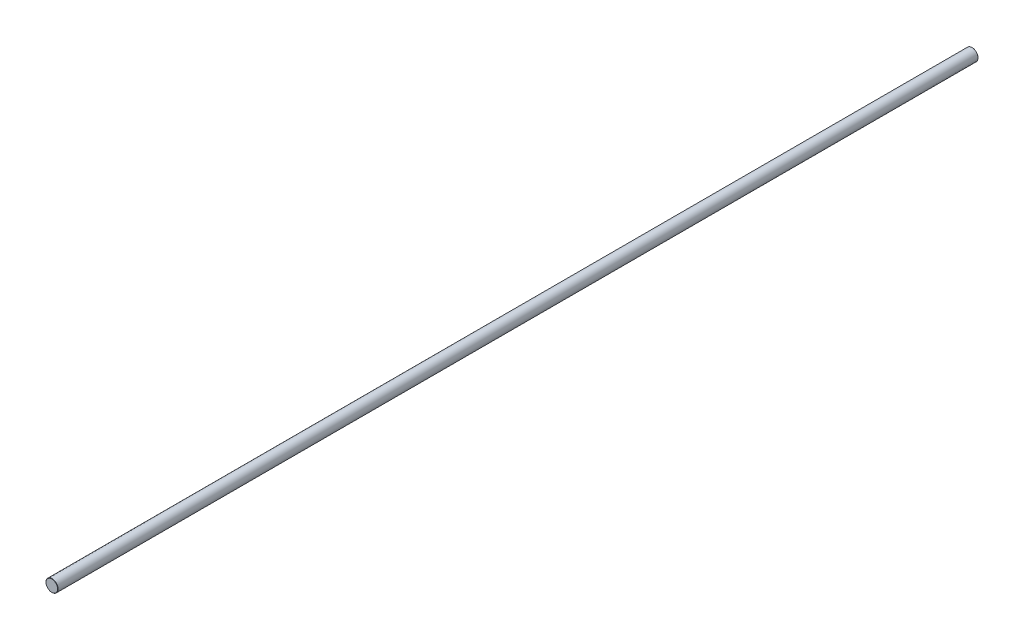
SolidWorks part; units mm, degrees
material "AISI 1045 Steel, cold drawn"
ref_plane "Front Plane" through (0, 0, 0) normal (0, 0, 1) x (1, 0, 0)
ref_plane "Top Plane" through (0, 0, 0) normal (0, 1, 0) x (1, 0, 0)
ref_plane "Right Plane" through (0, 0, 0) normal (1, 0, 0) x (0, 0, -1)
sketch "Sketch1" plane through (0, 0, 0) normal (0, 0, 1) x (1, 0, 0)
  circle A0 centre (0, 0) radius 8 construction
  dimension "Diameter" = 16
sketch "Sketch2" plane through (0, 0, 0) normal (1, 0, 0) x (0, 0, -1)
  line L0 (610, 0) -> (-610, 0) construction
  point P0 (-488, 0)
  point P3 (0, 0)
  point P4 (488, 0)
  point P6 (-427, 0)
  point P7 (427, 0)
  dimension "Length" = 1220
  dimension "D1" = 122
  dimension "D2" = 122
  dimension "D3" = 183
  dimension "D4" = 183
sketch "Sketch3" plane through (0, 0, 0) normal (0, 0, 1) x (1, 0, 0)
  circle A0 centre (0, 0) radius 8 construction
  circle A1 centre (0, 0) radius 8
extrude "Boss-Extrude1" add sketch "Sketch3" along normal up to vertex (610 mm away) and the other way up to vertex (610 mm away) up to point (0, 0, 610) other way up to point (0, 0, -610)
chamfer "Chamfer1" distance 0.32 angle 45 2 edges at (8, 0, 610) (8, 0, -610)
equation "\"D1@Chamfer1\"=\"Diameter@Sketch1\"*.02"
equation "\"D1@Sketch2\"=\"D2@Sketch2\""
equation "\"D2@Sketch2\"=\"Length@Sketch2\"*.1"
equation "\"D3@Sketch2\"=\"Length@Sketch2\"*.15"
equation "\"D4@Sketch2\"=\"D3@Sketch2\""
